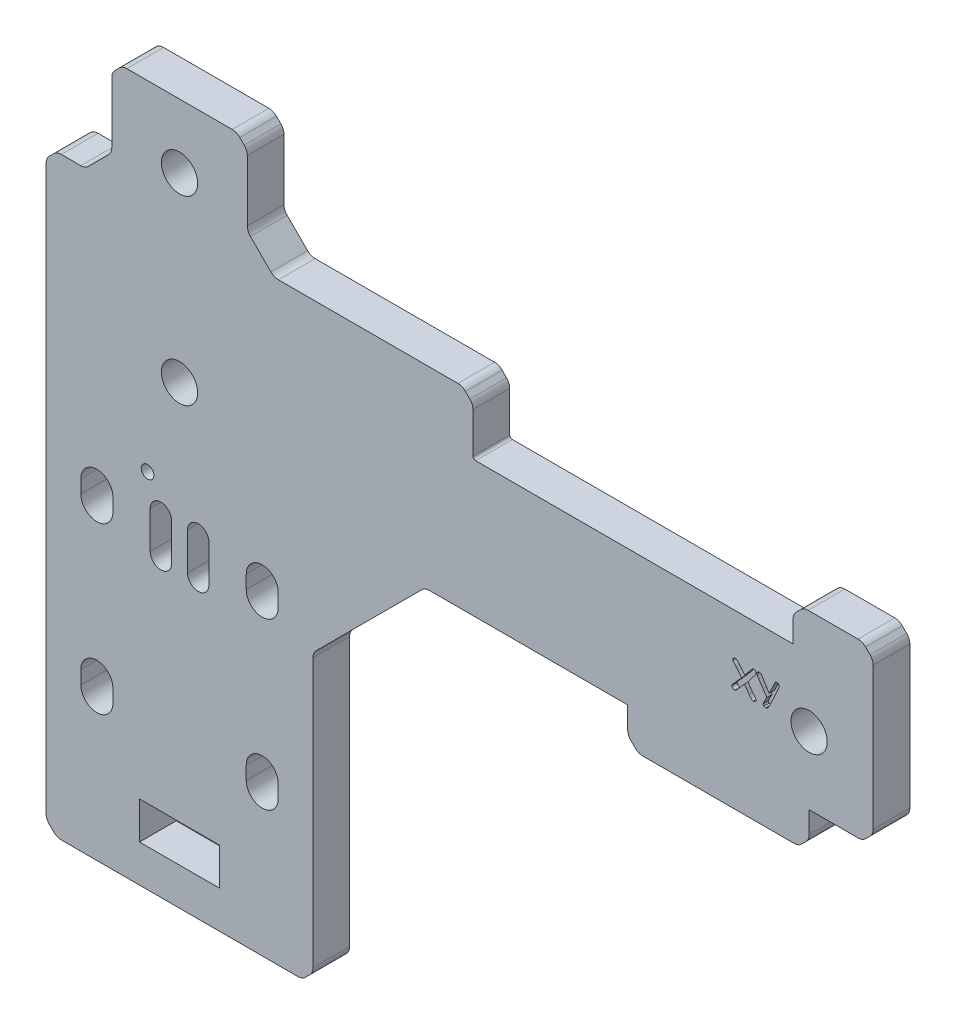
SolidWorks part; units mm, degrees
ref_plane "Front Plane" through (0, 0, 0) normal (0, 0, 1) x (1, 0, 0)
ref_plane "Top Plane" through (0, 0, 0) normal (0, 1, 0) x (1, 0, 0)
ref_plane "Right Plane" through (0, 0, 0) normal (1, 0, 0) x (0, 0, -1)
sketch "Sketch1" plane through (0, 0, 0) normal (0, 0, 1) x (1, 0, 0)
  line L1 (25, -65.675) -> (-25, -65.675)
  line L2 (25, -65.675) -> (25, 65.675)
  line L3 (25, 65.675) -> (-25, 65.675)
  line L4 (-25, -65.675) -> (-25, 65.675)
  line L5 (25, -65.675) -> (-25, 65.675) construction
  line L6 (25, 65.675) -> (-25, -65.675) construction
  point P0 (0, 0)
  dimension "D1" = 50
  dimension "D2" = 131.35
extrude "Boss-Extrude1" add sketch "Sketch1" along normal blind 6.88
sketch "Sketch2" plane through (0, 0, 6.88) normal (0, 0, 1) x (1, 0, 0)
  line L1 (15.5, -36.175) -> (-15.5, -36.175) construction
  line L2 (15.5, -36.175) -> (15.5, -5.175) construction
  line L3 (15.5, -5.175) -> (-15.5, -5.175) construction
  line L4 (-15.5, -36.175) -> (-15.5, -5.175) construction
  line L5 (15.5, -36.175) -> (-15.5, -5.175) construction
  line L6 (15.5, -5.175) -> (-15.5, -36.175) construction
  line L7 (-25, -65.675) -> (25, -65.675) construction
  line L8 (25, 65.675) -> (-25, 65.675) construction
  circle A0 centre (0, -20.675) radius 11.075
  circle A1 centre (-15.5, -5.175) radius 1.75
  circle A2 centre (-15.5, -36.175) radius 1.75
  circle A3 centre (15.5, -36.175) radius 1.75
  circle A4 centre (15.5, -5.175) radius 1.75
  circle A5 centre (0, 53.675) radius 3.4
  circle A6 centre (0, 19.675) radius 3.4
  dimension "D3" = 3.5
  dimension "D4" = 22.15
  dimension "D7" = 6.8
  dimension "D1" = 31
  dimension "D2" = 45
  dimension "D5" = 34
  dimension "D6" = 12
extrude "Cut-Extrude1" cut sketch "Sketch2" against normal through all
sketch "Sketch3" plane through (0, 0, 6.88) normal (0, 0, 1) x (1, 0, 0)
  line L0 (-25, -65.675) -> (25, -65.675) construction
  line L1 (7.5, -51.675) -> (-7.5, -51.675)
  line L2 (7.5, -51.675) -> (7.5, -58.675)
  line L3 (7.5, -58.675) -> (-7.5, -58.675)
  line L4 (-7.5, -51.675) -> (-7.5, -58.675)
  line L5 (7.5, -51.675) -> (-7.5, -58.675) construction
  line L6 (7.5, -58.675) -> (-7.5, -51.675) construction
  point P0 (0, -55.175)
  dimension "D1" = 15
  dimension "D2" = 7
  dimension "D3" = 7
extrude "Cut-Extrude2" cut sketch "Sketch3" against normal blind 6.88
sketch "Sketch4" plane through (0, 0, 6.88) normal (0, 0, 1) x (1, 0, 0)
  line L0 (25, 9.325) -> (130, 9.325)
  line L1 (25, -65.675) -> (25, 65.675) construction
  line L2 (130, 9.325) -> (130, 34.725)
  line L3 (130, 34.725) -> (25, 34.725)
  line L4 (25, 34.725) -> (25, 9.325)
  line L5 (-25, 65.675) -> (-25, -65.675) construction
  line L6 (130, 22.025) -> (0, 22.025) construction
  line L7 (-25, -65.675) -> (25, -65.675) construction
  dimension "D1" = 25.4
  dimension "D2" = 155
  dimension "D3" = 75
extrude "Boss-Extrude2" add sketch "Sketch4" against normal up to vertex (6.88 mm away)
sketch "Sketch5" plane through (0, 0, 6.88) normal (0, 0, 1) x (1, 0, 0)
  line L0 (118, 22.025) -> (84, 22.025) construction
  line L1 (84, 22.025) -> (0, 22.025) construction
  line L2 (130, 9.325) -> (130, 34.725) construction
  circle A0 centre (118, 22.025) radius 3.4
  circle A1 centre (84, 22.025) radius 3.4
  point P8 (130, 22.025)
  dimension "D3" = 6.8
  dimension "D1" = 12
  dimension "D2" = 34
extrude "Cut-Extrude3" cut sketch "Sketch5" against normal blind 6.88
sketch "Sketch6" plane through (0, 0, 6.88) normal (0, 0, 1) x (1, 0, 0)
  line L0 (25, 9.325) -> (130, 9.325) construction
  line L1 (84, 9.325) -> (118, 9.325)
  line L2 (84, 9.325) -> (84, 2.445)
  line L3 (84, 2.445) -> (118, 2.445)
  line L4 (118, 9.325) -> (118, 2.445)
  line L5 (84, 34.725) -> (84, 9.325) construction
  line L6 (118, 22.025) -> (118, 9.325) construction
  line L7 (130, 34.725) -> (25, 34.725) construction
  line L8 (130, 34.725) -> (115, 34.725)
  line L9 (130, 34.725) -> (130, 41.605)
  line L10 (130, 41.605) -> (115, 41.605)
  line L11 (115, 34.725) -> (115, 41.605)
  dimension "D1" = 6.88
  dimension "D2" = 15
  dimension "D3" = 34
extrude "Boss-Extrude3" add sketch "Sketch6" against normal up to vertex (6.88 mm away)
sketch "Sketch7" plane through (0, 0, 6.88) normal (0, 0, 1) x (1, 0, 0)
  line L0 (-25, 65.675) -> (-25, -65.675) construction
  line L5 (115, 34.725) -> (25, 34.725) construction
  line L8 (-25, 65.675) -> (-12.7, 65.675)
  line L9 (-25, 65.675) -> (-25, 45.605)
  line L10 (-25, 45.605) -> (-12.7, 45.605)
  line L11 (-12.7, 65.675) -> (-12.7, 45.605)
  line L12 (25, 65.675) -> (12.7, 65.675)
  line L13 (25, 65.675) -> (25, 45.605)
  line L14 (25, 45.605) -> (12.7, 45.605)
  line L15 (12.7, 65.675) -> (12.7, 45.605)
  dimension "D1" = 25.4
  dimension "D2" = 10.88
extrude "Cut-Extrude4" cut sketch "Sketch7" against normal blind 6.88
sketch "Sketch8" plane through (0, 0, 6.88) normal (0, 0, 1) x (1, 0, 0)
  line L0 (-6, 2.175) -> (6, 2.175) construction
  line L1 (12.7, 65.675) -> (-12.7, 65.675) construction
  line L2 (130, 9.325) -> (130, 41.605) construction
  line L3 (41.1, 28.025) -> (41.1, 16.025) construction
  line L4 (41.1, 22.025) -> (118, 22.025) construction
  circle A0 centre (-6, 2.175) radius 1.1811
  circle A1 centre (6, 2.175) radius 1.1811 construction
  circle A2 centre (41.1, 28.025) radius 1.1811 construction
  circle A3 centre (41.1, 16.025) radius 1.1811 construction
  point P4 (0, 2.175)
  dimension "D1" = 2.3622
  dimension "D2" = 12
  dimension "D3" = 63.5
  dimension "D4" = 12
  dimension "D5" = 88.9
extrude "Cut-Extrude5" cut sketch "Sketch8" against normal blind 6.88
sketch "Sketch9" plane through (0, 0, 6.88) normal (0, 0, 1) x (1, 0, 0)
  circle A0 centre (15.5, -36.175) radius 3
  circle A1 centre (-15.5, -36.175) radius 3
  circle A2 centre (-15.5, -5.175) radius 3
  circle A4 centre (15.5, -5.175) radius 3
  dimension "D1" = 6
extrude "Cut-Extrude6" cut sketch "Sketch9" against normal blind 6.88
sketch "Sketch10" plane through (0, 0, 6.88) normal (0, 0, 1) x (1, 0, 0)
  circle A0 centre (0, -20.675) radius 13
  dimension "D1" = 26
extrude "Boss-Extrude4" add sketch "Sketch10" against normal up to vertex (6.88 mm away)
sketch "Sketch11" plane through (0, 0, 6.88) normal (0, 0, 1) x (1, 0, 0)
  line L0 (115, 34.725) -> (25, 34.725) construction
  line L1 (25, 45.605) -> (55, 45.605)
  line L2 (25, 45.605) -> (25, 34.725)
  line L3 (25, 34.725) -> (55, 34.725)
  line L4 (55, 45.605) -> (55, 34.725)
  dimension "D1" = 30
extrude "Boss-Extrude5" add sketch "Sketch11" against normal up to vertex (6.88 mm away)
chamfer "Chamfer2" distance 21 angle 45 1 edges at (25, 9.325, 3.44)
sketch "Sketch12" [suppressed] plane through (0, 0, 6.88) normal (0, 0, 1) x (1, 0, 0)
  line L0 (-15.5, -5.175) -> (-15.5, -7.675) construction
  line L1 (-13.75, -5.175) -> (-13.75, -7.675)
  line L2 (-17.25, -5.175) -> (-17.25, -7.675)
  line L3 (15.5, -5.175) -> (15.5, -7.675) construction
  line L4 (17.25, -5.175) -> (17.25, -7.675)
  line L5 (13.75, -5.175) -> (13.75, -7.675)
  line L6 (-15.5, -36.175) -> (-15.5, -38.675) construction
  line L7 (-13.75, -36.175) -> (-13.75, -38.675)
  line L8 (-17.25, -36.175) -> (-17.25, -38.675)
  line L9 (15.5, -36.175) -> (15.5, -38.675) construction
  line L10 (17.25, -36.175) -> (17.25, -38.675)
  line L11 (13.75, -36.175) -> (13.75, -38.675)
  line L12 (0, -20.675) -> (0, -23.175) construction
  line L13 (11.075, -20.675) -> (11.075, -23.175)
  line L14 (-11.075, -20.675) -> (-11.075, -23.175)
  arc A0 (-13.75, -5.175) -> (-17.25, -5.175) centre (-15.5, -5.175) ccw
  arc A1 (-17.25, -7.675) -> (-13.75, -7.675) centre (-15.5, -7.675) ccw
  circle A2 centre (-15.5, -5.175) radius 1.75 construction
  arc A3 (17.25, -5.175) -> (13.75, -5.175) centre (15.5, -5.175) ccw
  arc A4 (13.75, -7.675) -> (17.25, -7.675) centre (15.5, -7.675) ccw
  arc A5 (-13.75, -36.175) -> (-17.25, -36.175) centre (-15.5, -36.175) ccw
  arc A6 (-17.25, -38.675) -> (-13.75, -38.675) centre (-15.5, -38.675) ccw
  arc A7 (17.25, -36.175) -> (13.75, -36.175) centre (15.5, -36.175) ccw
  arc A8 (13.75, -38.675) -> (17.25, -38.675) centre (15.5, -38.675) ccw
  arc A9 (11.075, -20.675) -> (-11.075, -20.675) centre (0, -20.675) ccw
  arc A10 (-11.075, -23.175) -> (11.075, -23.175) centre (0, -23.175) ccw
  circle A11 centre (0, -20.675) radius 11.075 construction
  point P3 (-15.5, -6.425)
  point P12 (15.5, -6.425)
  point P19 (-15.5, -37.425)
  point P26 (15.5, -37.425)
  point P35 (0, -21.925)
  dimension "D1" = 2.5
  dimension "D2" = 2.5
extrude "Cut-Extrude7" [suppressed] cut sketch "Sketch12" against normal blind 10
sketch "Sketch13" plane through (0, 0, 6.88) normal (0, 0, 1) x (1, 0, 0)
  line L0 (-15.5, -5.175) -> (-15.5, -7.675) construction
  line L1 (-12.5, -5.175) -> (-12.5, -7.675)
  line L2 (-18.5, -5.175) -> (-18.5, -7.675)
  line L3 (15.5, -5.175) -> (15.5, -7.675) construction
  line L4 (18.5, -5.175) -> (18.5, -7.675)
  line L5 (12.5, -5.175) -> (12.5, -7.675)
  line L6 (15.5, -36.175) -> (15.5, -38.675) construction
  line L7 (18.5, -36.175) -> (18.5, -38.675)
  line L8 (12.5, -36.175) -> (12.5, -38.675)
  line L9 (-15.5, -36.175) -> (-15.5, -38.675) construction
  line L10 (-12.5, -36.175) -> (-12.5, -38.675)
  line L11 (-18.5, -36.175) -> (-18.5, -38.675)
  arc A0 (-12.5, -5.175) -> (-18.5, -5.175) centre (-15.5, -5.175) ccw
  arc A1 (-18.5, -7.675) -> (-12.5, -7.675) centre (-15.5, -7.675) ccw
  circle A2 centre (-15.5, -5.175) radius 3 construction
  arc A3 (18.5, -5.175) -> (12.5, -5.175) centre (15.5, -5.175) ccw
  arc A4 (12.5, -7.675) -> (18.5, -7.675) centre (15.5, -7.675) ccw
  arc A5 (18.5, -36.175) -> (12.5, -36.175) centre (15.5, -36.175) ccw
  arc A6 (12.5, -38.675) -> (18.5, -38.675) centre (15.5, -38.675) ccw
  arc A7 (-12.5, -36.175) -> (-18.5, -36.175) centre (-15.5, -36.175) ccw
  arc A8 (-18.5, -38.675) -> (-12.5, -38.675) centre (-15.5, -38.675) ccw
  point P3 (-15.5, -6.425)
  point P12 (15.5, -6.425)
  point P19 (15.5, -37.425)
  point P26 (-15.5, -37.425)
  dimension "D1" = 2.5
extrude "Cut-Extrude8" cut sketch "Sketch13" against normal blind 10
sketch "Sketch14" plane through (0, 0, 6.88) normal (0, 0, 1) x (1, 0, 0)
  line L0 (3.5, -7) -> (-3.5, -7) construction
  line L1 (3.5, -9) -> (-3.5, -9) construction
  line L2 (3.5, -5) -> (-3.5, -5) construction
  line L3 (-3.5, -10.5) -> (-3.5, -3.5) construction
  line L4 (-5.5, -10.5) -> (-5.5, -3.5)
  line L5 (-1.5, -10.5) -> (-1.5, -3.5)
  line L6 (3.5, -10.5) -> (3.5, -3.5) construction
  line L7 (1.5, -10.5) -> (1.5, -3.5)
  line L8 (5.5, -10.5) -> (5.5, -3.5)
  arc A0 (3.5, -9) -> (3.5, -5) centre (3.5, -7) ccw construction
  arc A1 (-3.5, -5) -> (-3.5, -9) centre (-3.5, -7) ccw construction
  arc A2 (-5.5, -10.5) -> (-1.5, -10.5) centre (-3.5, -10.5) ccw
  arc A3 (-1.5, -3.5) -> (-5.5, -3.5) centre (-3.5, -3.5) ccw
  arc A4 (1.5, -10.5) -> (5.5, -10.5) centre (3.5, -10.5) ccw
  arc A5 (5.5, -3.5) -> (1.5, -3.5) centre (3.5, -3.5) ccw
  point P2 (0, -7)
  point P10 (-3.5, -7)
  point P16 (3.5, -7)
  dimension "D1" = 4
  dimension "D2" = 7
  dimension "D3" = 7
extrude "Cut-Extrude9" cut sketch "Sketch14" against normal through all
chamfer "Chamfer5" distance 5 angle 45 2 edges at (-12.7, 45.605, 3.44) (12.7, 45.605, 3.44)
chamfer "Chamfer3" distance 2 angle 45 11 edges at (-25, -65.675, 3.44) (84, 2.445, 3.44) (118, 2.445, 3.44) (130, 9.325, 3.44) (115, 41.605, 3.44) (130, 41.605, 3.44) (-25, 45.605, 3.44) (-12.7, 65.675, 3.44) (12.7, 65.675, 3.44) (55, 45.605, 3.44) (25, -65.675, 3.44)
sketch "Sketch15" plane through (0, 0, 6.88) normal (0, 0, 1) x (1, 0, 0)
  circle A0 centre (84, 22.025) radius 7.2715
extrude "Boss-Extrude6" add sketch "Sketch15" against normal up to vertex (6.88 mm away)
sketch "Sketch16" [suppressed] plane through (0, 0, 6.88) normal (0, 0, 1) x (1, 0, 0)
  circle A0 centre (118, 22.025) radius 7.069
extrude "Boss-Extrude7" [suppressed] add sketch "Sketch16" against normal up to vertex
fillet "Fillet1" radius 2 28 edges at (17.7, 45.605, 3.44) (12.7, 50.605, 3.44) (12.7, 63.675, 3.44) (10.7, 65.675, 3.44) (-10.7, 65.675, 3.44) (-12.7, 63.675, 3.44) (-12.7, 50.605, 3.44) (-17.7, 45.605, 3.44) (-25, 43.605, 3.44) (-25, -63.675, 3.44) (-23, -65.675, 3.44) (23, -65.675, 3.44) (25, -63.675, 3.44) (25, -11.675, 3.44) (46, 9.325, 3.44) (84, 4.445, 3.44) (86, 2.445, 3.44) (116, 2.445, 3.44) (118, 4.445, 3.44) (128, 9.325, 3.44) (130, 11.325, 3.44) (130, 39.605, 3.44) (128, 41.605, 3.44) (117, 41.605, 3.44) (115, 39.605, 3.44) (55, 43.605, 3.44) (53, 45.605, 3.44) (-23, 45.605, 3.44)
fillet "Fillet2" [suppressed] radius 2
fillet "Fillet3" radius 0.5 1 edges at (55, 34.725, 3.44)
fillet "Fillet4" [suppressed] radius 0.5
sketch "Sketch17" [suppressed] plane through (0, 0, 0) normal (0, 0, -1) x (-1, 0, 0)
  line L2 (-11.075, -20.675) -> (-11.075, -23.175)
  line L3 (11.075, -23.175) -> (11.075, -20.675)
  line L4 (-11.075, -20.675) -> (-11.075, -23.175) construction
  line L5 (11.075, -23.175) -> (11.075, -20.675) construction
  arc A1 (11.575, -20.675) -> (-11.575, -20.675) centre (0, -20.675) ccw construction
  arc A3 (-11.075, -23.175) -> (11.075, -23.175) centre (0, -23.175) ccw
  arc A4 (11.075, -20.675) -> (-11.075, -20.675) centre (0, -20.675) ccw
  arc A5 (-11.075, -23.175) -> (11.075, -23.175) centre (0, -23.175) ccw construction
  arc A6 (11.075, -20.675) -> (-11.075, -20.675) centre (0, -20.675) ccw construction
  text T0 "STEPPER MOTOR" font "Comic Sans MS" height 3
  dimension "D1" = 0
  dimension "D2" = 0.5
extrude "Cut-Extrude10" [suppressed] cut sketch "Sketch17" against normal blind 1
sketch "Sketch18" plane through (0, 0, 6.88) normal (0, 0, 1) x (1, 0, 0)
  line L0 (118, 22.025) -> (98, 22.025) construction
  text T0 "XY" font "Comic Sans MS" height 5
  dimension "D1" = 20
extrude "Cut-Extrude11" cut sketch "Sketch18" against normal blind 1
sketch "Sketch19" [suppressed] plane through (0, 0, 0) normal (0, 0, -1) x (-1, 0, 0)
  line L0 (-84, 22.025) -> (-104, 22.025) construction
  text T0 "XY" font "Comic Sans MS" height 5
  dimension "D1" = 20
extrude "Cut-Extrude12" [suppressed] cut sketch "Sketch19" against normal blind 1
